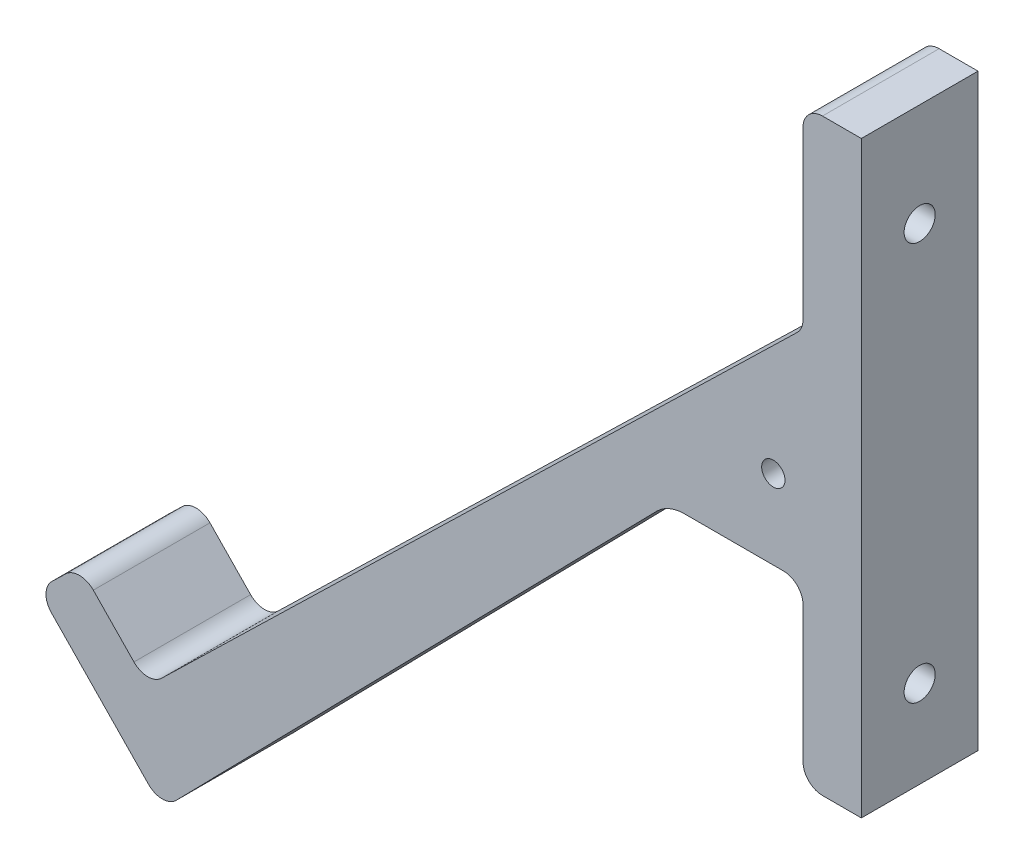
SolidWorks part; units mm, degrees
material "Plastique personnalisé"
ref_plane "Plan de face" through (0, 0, 0) normal (0, 0, 1) x (1, 0, 0)
ref_plane "Plan de dessus" through (0, 0, 0) normal (0, 1, 0) x (1, 0, 0)
ref_plane "Plan de droite" through (0, 0, 0) normal (1, 0, 0) x (0, 0, -1)
sketch "Esquisse1" plane through (0, 0, 0) normal (0, 0, 1) x (1, 0, 0)
  line L0 (-1.5166, -1.4728) -> (-164.9995, -160.2347)
  line L1 (0, 2.1141) -> (0, 45)
  line L2 (5, 50) -> (15, 50)
  line L3 (15, 50) -> (15, -6.3423)
  line L4 (0, 0) -> (10.4501, -10.7608) construction
  line L5 (-10.4198, -10.1189) -> (0.0303, -20.8797) construction
  line L6 (-179.3473, -174.1682) -> (-168.3523, -185.4901)
  line L7 (-161.1931, -185.5052) -> (-37.6405, -59.3455)
  line L9 (15, -6.3423) -> (15, -51.3423)
  line L10 (10, -56.3423) -> (-30.496, -56.3423)
  line L11 (-179.3473, -174.1682) -> (-193.284, -159.817)
  line L12 (-193.1804, -152.7467) -> (-189.5935, -149.2633)
  line L13 (-182.5232, -149.3669) -> (-172.0698, -160.1311)
  arc A0 (-30.496, -56.3423) -> (-37.6405, -59.3455) centre (-30.496, -66.3423) ccw
  arc A1 (0, 45) -> (5, 50) centre (5, 45) cw
  arc A2 (-1.5166, -1.4728) -> (0, 2.1141) centre (-5, 2.1141) ccw
  arc A3 (15, -51.3423) -> (10, -56.3423) centre (10, -51.3423) cw
  arc A4 (-168.3523, -185.4901) -> (-161.1931, -185.5052) centre (-164.7654, -182.0067) ccw
  arc A5 (-193.284, -159.817) -> (-193.1804, -152.7467) centre (-189.6971, -156.3336) cw
  arc A6 (-189.5935, -149.2633) -> (-182.5232, -149.3669) centre (-186.1101, -152.8503) cw
  arc A7 (-172.0698, -160.1311) -> (-164.9995, -160.2347) centre (-168.4829, -156.6478) ccw
  point P19 (0, 50)
  point P25 (15, -56.3423)
  point P28 (-164.7804, -189.1682)
  point P31 (-196.7674, -156.2301)
  point P34 (-186.0066, -145.78)
  dimension "D7" = 10
  dimension "D9" = 5
  dimension "D1" = 250
  dimension "D2" = 50
  dimension "D3" = 15
  dimension "D4" = 15
  dimension "D5" = 15
  dimension "D6" = 50
  dimension "D8" = 15
extrude "Boss.-Extru.3" add sketch "Esquisse1" along normal blind 30
sketch "Esquisse2" plane through (0, 0, 0) normal (0, 0, 1) x (1, 0, 0)
  line L1 (15, -51.3423) -> (0, -51.3423)
  line L2 (15, -51.3423) -> (15, -101.3423)
  line L3 (15, -101.3423) -> (0, -101.3423)
  line L4 (0, -51.3423) -> (0, -101.3423)
  dimension "D1" = 50
  dimension "D2" = 15
extrude "Boss.-Extru.4" add sketch "Esquisse2" along normal blind 30
fillet "Congé1" radius 5 2 edges at (0, -101.3423, 15) (0, -56.3423, 15)
sketch "Esquisse3" plane through (0, 0, 0) normal (-1, 0, 0) x (0, 0, 1)
  line L0 (0, 45) -> (30, 2.1141) construction
  circle A0 centre (15, 23.5571) radius 4
extrude "Enlèv. mat.-Extru.1" cut sketch "Esquisse3" against normal blind 30
sketch "Esquisse4" plane through (0, 0, 0) normal (-1, 0, 0) x (0, 0, 1)
  line L0 (0, -61.3423) -> (30, -96.3423) construction
  circle A0 centre (15, -78.8423) radius 4
extrude "Enlèv. mat.-Extru.2" cut sketch "Esquisse4" against normal blind 30
fillet "Congé2" radius 0.5 2 edges at (0, 23.5571, 19) (0, -82.8423, 15)
sketch "Esquisse5" plane through (0, 0, 30) normal (0, 0, 1) x (1, 0, 0)
  circle A0 centre (-7.6372, -35.9569) radius 3
extrude "Enlèv. mat.-Extru.3" cut sketch "Esquisse5" against normal blind 30
